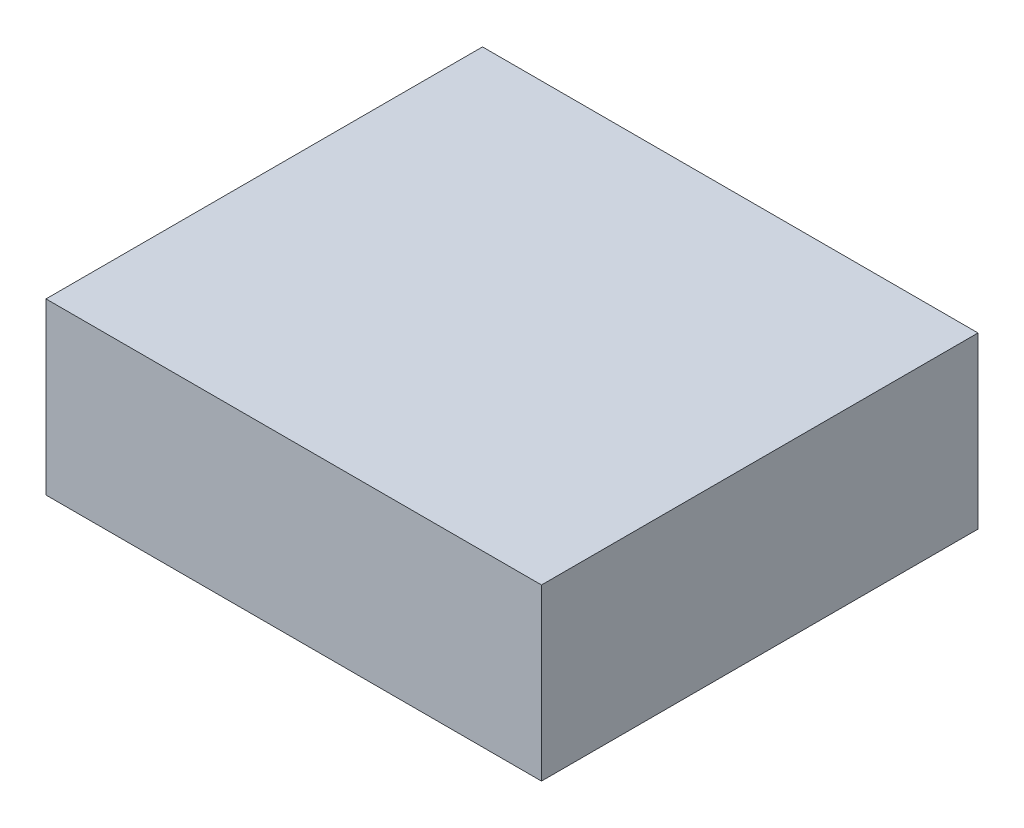
SolidWorks part; units mm, degrees
ref_plane "Front Plane" through (0, 0, 0) normal (0, 0, 1) x (1, 0, 0)
ref_plane "Top Plane" through (0, 0, 0) normal (0, 1, 0) x (1, 0, 0)
ref_plane "Right Plane" through (0, 0, 0) normal (1, 0, 0) x (0, 0, -1)
sketch "Sketch1" plane through (0, 0, 0) normal (0, 0, 1) x (1, 0, 0)
  line L1 (0, 0) -> (105, 0)
  line L2 (0, 0) -> (0, 36)
  line L3 (0, 36) -> (105, 36)
  line L4 (105, 0) -> (105, 36)
  dimension "D1" = 36
  dimension "D2" = 105
extrude "Boss-Extrude1" add sketch "Sketch1" along normal blind 92.5
